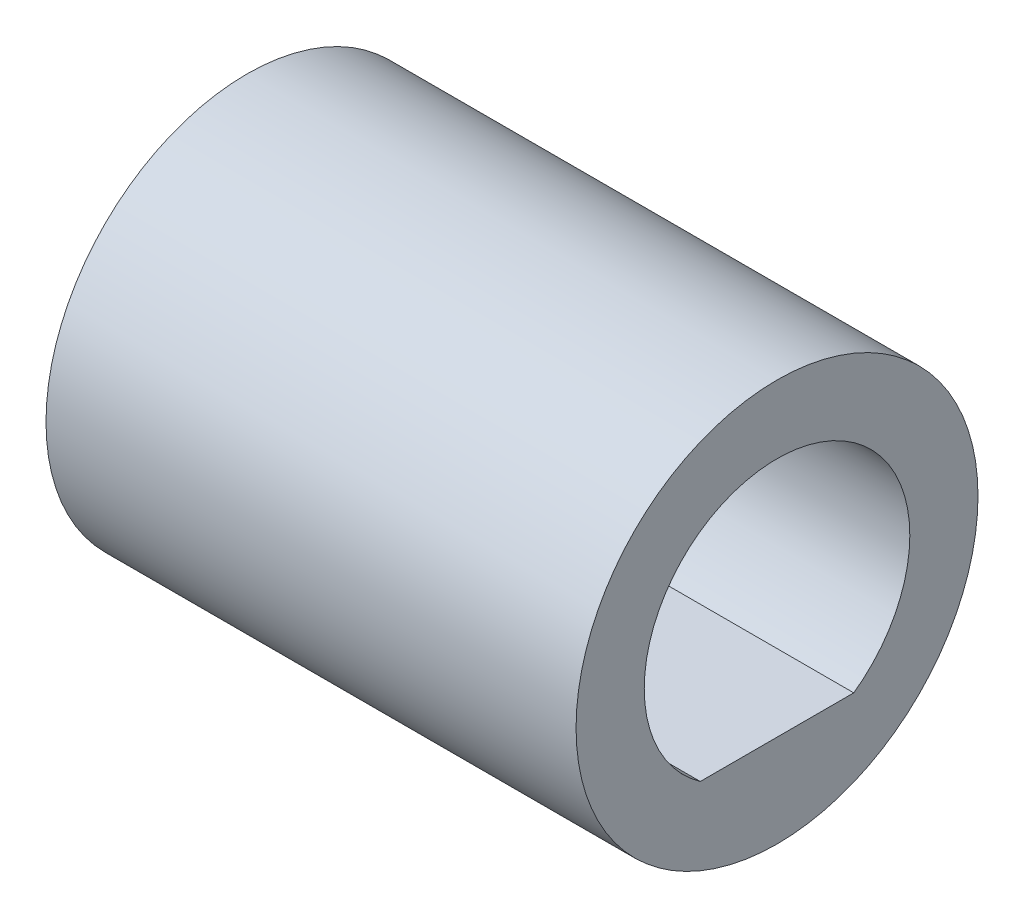
SolidWorks part; units mm, degrees
ref_plane "Front Plane" through (0, 0, 0) normal (0, 0, 1) x (1, 0, 0)
ref_plane "Top Plane" through (0, 0, 0) normal (0, 1, 0) x (1, 0, 0)
ref_plane "Right Plane" through (0, 0, 0) normal (1, 0, 0) x (0, 0, -1)
sketch "Sketch1" plane through (0, 0, 0) normal (1, 0, 0) x (0, 0, -1)
  line L0 (-1.5274, -2.157) -> (1.5274, -2.157) construction
  line L1 (-1.5274, -2.157) -> (1.5274, -2.157)
  arc A0 (1.5274, -2.157) -> (-1.5274, -2.157) centre (0, 0) ccw construction
  arc A1 (1.5274, -2.157) -> (-1.5274, -2.157) centre (0, 0) ccw
  circle A2 centre (0, 0) radius 4
  dimension "D1" = 8
extrude "Boss-Extrude1" add sketch "Sketch1" along normal offset from surface (10.55 mm away) 0.25
